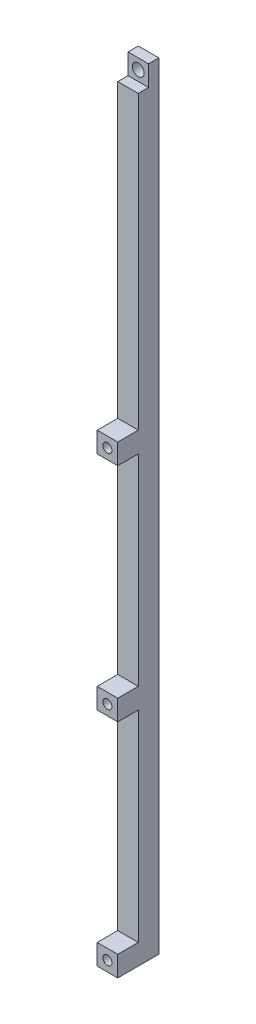
SolidWorks part; units mm, degrees
ref_plane "Front Plane" through (0, 0, 0) normal (0, 0, 1) x (1, 0, 0)
ref_plane "Top Plane" through (0, 0, 0) normal (0, 1, 0) x (1, 0, 0)
ref_plane "Right Plane" through (0, 0, 0) normal (1, 0, 0) x (0, 0, -1)
sketch "Sketch1" plane through (0, 0, 0) normal (0, 1, 0) x (1, 0, 0)
  line L1 (0, 0) -> (6.35, 0)
  line L2 (0, 0) -> (0, 12.7)
  line L3 (0, 12.7) -> (6.35, 12.7)
  line L4 (6.35, 0) -> (6.35, 12.7)
  dimension "D1" = 6.35
  dimension "D2" = 12.7
extrude "Boss-Extrude1" add sketch "Sketch1" along normal blind 240.03
sketch "Sketch2" plane through (0, 0, 0) normal (-1, 0, 0) x (0, 0, 1)
  line L0 (0, 240.03) -> (0, 0) construction
  line L1 (0, 240.03) -> (-9.525, 240.03)
  line L2 (0, 240.03) -> (0, 233.68)
  line L3 (0, 233.68) -> (-9.525, 233.68)
  line L4 (-9.525, 240.03) -> (-9.525, 233.68)
  line L5 (-12.7, 0) -> (0, 0) construction
  line L6 (0, 143.51) -> (-6.35, 143.51)
  line L7 (0, 143.51) -> (0, 233.68)
  line L9 (-6.35, 143.51) -> (-6.35, 233.68)
  line L10 (0, 137.16) -> (-6.35, 137.16)
  line L11 (0, 137.16) -> (0, 74.93)
  line L12 (0, 74.93) -> (-6.35, 74.93)
  line L13 (-6.35, 137.16) -> (-6.35, 74.93)
  line L14 (0, 68.58) -> (-6.35, 68.58)
  line L15 (0, 68.58) -> (0, 6.35)
  line L16 (0, 6.35) -> (-6.35, 6.35)
  line L17 (-6.35, 68.58) -> (-6.35, 6.35)
  line M2 (0, 0) -> (0, 240.03)
  line M3 (0, 240.03) -> (-12.7, 240.03)
  dimension "D1" = 9.525
  dimension "D2" = 6.35
  dimension "D3" = 6.35
  dimension "D4" = 6.35
  dimension "D5" = 6.35
  dimension "D6" = 90.17
  dimension "D7" = 6.35
  dimension "D8" = 62.23
  dimension "D9" = 6.35
  dimension "D10" = 62.23
  dimension "D11" = 6.35
extrude "Cut-Extrude-Thin1" cut sketch "Sketch2" against normal through all thin contours L4 L3 M3 M2 | L15 L16 L17 L14 | L11 L12 L13 L10 | L9 L6 L7
hole_wizard "#35 (0.11) Diameter Hole1" positions "Sketch5" profile "Sketch4" hole size "#35" standard "ANSI Inch" end condition through all
sketch "Sketch5" plane through (0, 0, 0) normal (0, 0, 1) x (1, 0, 0)
  line L0 (3.175, 240.03) -> (3.175, 0) construction
  line L1 (0, 240.03) -> (6.35, 240.03) construction
  line L2 (0, 0) -> (6.35, 0) construction
  line L3 (3.175, 0) -> (6.35, 3.1749) construction
  line L4 (6.35, 6.3499) -> (6.35, 0) construction
  line L5 (6.35, 3.1749) -> (0, 3.1749) construction
  line L6 (0, 6.3499) -> (0, 0) construction
  line L7 (0, 3.1749) -> (6.35, 71.755) construction
  line L8 (6.35, 74.9299) -> (6.35, 68.5801) construction
  line L9 (6.35, 71.755) -> (0, 71.755) construction
  line L10 (0, 74.9299) -> (0, 68.5801) construction
  line L11 (0, 71.755) -> (6.35, 140.335) construction
  line L12 (6.35, 143.5099) -> (6.35, 137.1601) construction
  line L13 (6.35, 140.335) -> (0, 140.335) construction
  line L14 (0, 143.5099) -> (0, 137.1601) construction
  line L15 (0, 140.335) -> (6.35, 236.8549) construction
  line L16 (6.35, 240.03) -> (6.35, 233.6799) construction
  line L17 (6.35, 236.8549) -> (0, 236.8549) construction
  line L18 (0, 240.03) -> (0, 233.6799) construction
  point P43 (3.175, 140.335)
  point P45 (3.175, 71.755)
  point P47 (3.175, 3.1749)
sketch "Sketch4" plane through (3.175, 140.335, 0) normal (1, 0, 0) x (0, -1, 0)
  line L0 (0, 0) -> (0, 12.7)
  line L1 (0, 12.7) -> (1.397, 12.7)
  line L2 (1.397, 12.7) -> (1.397, 0)
  line L5 (1.397, 0) -> (0, 0)
  line L11 (0, -6.35) -> (0, 107.95) construction
  dimension "Thru Hole Dia." = 2.794
  dimension "Thru Hole Depth" = 12.7
hole_wizard "#6 Clearance Hole1" positions "Sketch7" profile "Sketch6" hole size "#6" standard "ANSI Inch" end condition through all
sketch "Sketch7" plane through (0, 0, -9.5251) normal (0, 0, 1) x (1, 0, 0)
  line L0 (0, 236.8549) -> (6.35, 236.8549) construction
  line L1 (0, 240.03) -> (0, 233.6799) construction
  line L2 (6.35, 240.03) -> (6.35, 233.6799) construction
  line L3 (6.35, 236.8549) -> (3.175, 240.03) construction
  line L4 (0, 240.03) -> (6.35, 240.03) construction
  line L5 (3.175, 240.03) -> (3.175, 233.6799) construction
  line L6 (6.35, 233.6799) -> (0, 233.6799) construction
  point P17 (3.175, 236.8549)
sketch "Sketch6" plane through (3.175, 236.8549, -9.5251) normal (1, 0, 0) x (0, -1, 0)
  line L0 (0, 0) -> (0, 3.1749)
  line L1 (0, 3.1749) -> (1.8288, 3.1749)
  line L2 (1.8288, 3.1749) -> (1.8288, 0)
  line L5 (1.8288, 0) -> (0, 0)
  line L11 (0, -6.35) -> (0, 107.95) construction
  dimension "Thru Hole Dia." = 3.6576
  dimension "Thru Hole Depth" = 3.1749
